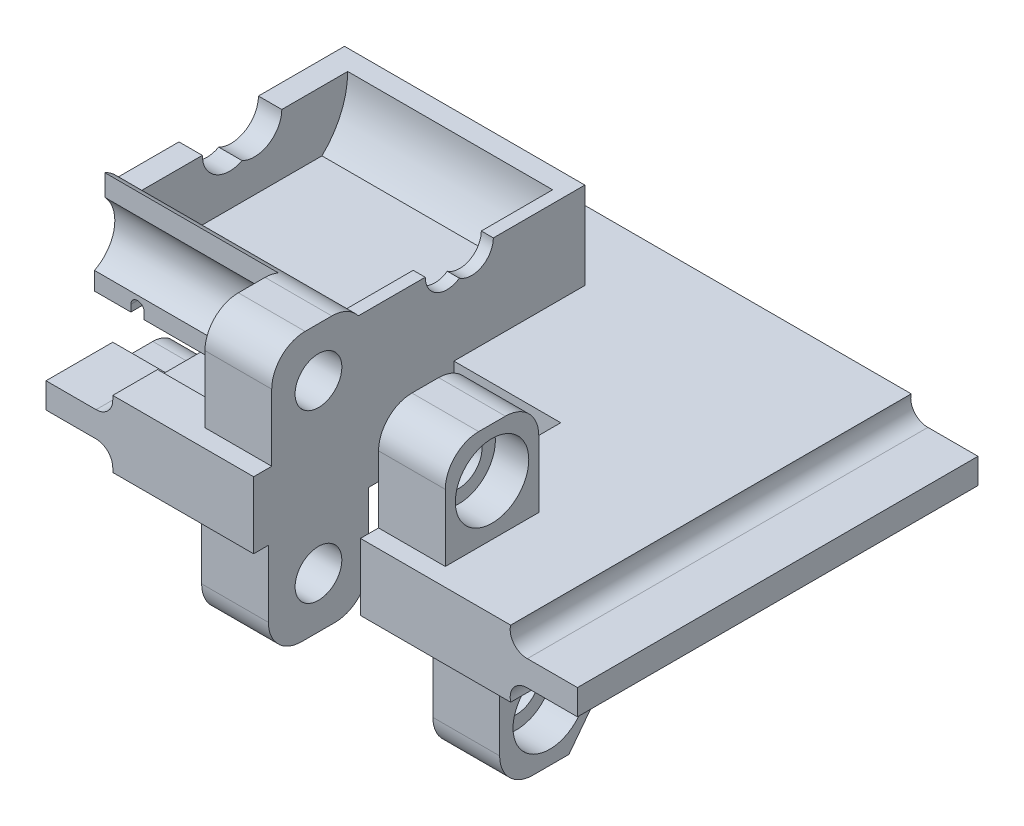
SolidWorks part; units mm, degrees
material "ABS"
ref_plane "정면" through (0, 0, 0) normal (0, 0, 1) x (1, 0, 0)
ref_plane "윗면" through (0, 0, 0) normal (0, 1, 0) x (1, 0, 0)
ref_plane "우측면" through (0, 0, 0) normal (1, 0, 0) x (0, 0, -1)
sketch "스케치1" plane through (0, 0, 0) normal (0, 0, 1) x (1, 0, 0)
  line L0 (0, 0) -> (0, 10)
  line L1 (29.8, 10) -> (-29.8, 10)
  line L2 (-32.3, 6.9) -> (-39.8, 6.9)
  line L3 (-39.8, 6.9) -> (-39.8, 3.1)
  line L4 (-39.8, 3.1) -> (-32.3, 3.1)
  line L5 (-29.8, 0) -> (29.8, 0)
  line L6 (39.8, 3.1) -> (32.3, 3.1)
  line L7 (39.8, 6.9) -> (39.8, 3.1)
  line L8 (32.3, 6.9) -> (39.8, 6.9)
  line L9 (-29.8, 10) -> (-29.8, 9.4)
  line L10 (-29.8, 0.6) -> (-29.8, 0)
  arc A2 (32.3, 3.1) -> (29.8, 0) centre (32.2267, 0.6011) ccw
  arc A3 (29.8, 10) -> (32.3, 6.9) centre (32.2267, 9.3989) ccw
  arc A5 (-32.3, 3.1) -> (-29.8, 0.6) centre (-32.3, 0.6) cw
  arc A6 (-29.8, 9.4) -> (-32.3, 6.9) centre (-32.3, 9.4) cw
  point P13 (0, 5)
  point P14 (-39.8, 5)
  dimension "D5" = 2.5
  dimension "D6" = 2.5
  dimension "D1" = 39.8
  dimension "D2" = 29.8
  dimension "D3" = 10
  dimension "D4" = 29.8
  dimension "D7" = 3.8
extrude "보스-돌출1" add sketch "스케치1" along normal blind 60
sketch "스케치2" plane through (-39.8, 0, 0) normal (-1, 0, 0) x (0, 0, 1)
  line L1 (44, 4) -> (50, 4)
  line L2 (50, 4) -> (50, 8)
  line L3 (16, 4) -> (10, 4)
  line L4 (50, 8) -> (10, 8)
  line L5 (30, 8) -> (30, 0)
  line L6 (20, 0) -> (40, 0)
  line L7 (60, 6.9) -> (60, 3.1) construction
  line L8 (10, 4) -> (10, 8)
  line L9 (60, 0) -> (0, 0) construction
  arc A0 (40, 0) -> (44, 4) centre (44, 0) cw
  arc A1 (20, 0) -> (16, 4) centre (16, 0) ccw
  line M12 (0, 3.1) -> (60, 3.1)
  line M14 (60, 6.9) -> (0, 6.9)
  dimension "D4" = 4
  dimension "D1" = 4
  dimension "D2" = 4
  dimension "D3" = 10
  dimension "D5" = 20
  dimension "D6" = 10
extrude "컷-돌출1" cut sketch "스케치2" against normal blind 17.3 contours A1 L5 L8 L3 M12 M14 | L6 A0 L5 M12 | A0 L1 L2 L5 M12 M14
sketch "Sketch1" plane through (0, 10, 0) normal (0, 1, 0) x (1, 0, 0)
  line L0 (29.8, -60) -> (-29.8, -60) construction
  line L1 (7.3, -60) -> (-8.7, -60)
  line L2 (7.3, -60) -> (7.3, -30)
  line L3 (7.3, -30) -> (-8.7, -30)
  line L4 (-8.7, -60) -> (-8.7, -30)
  line L5 (29.8, -60) -> (29.8, 0) construction
  dimension "D1" = 22.5
  dimension "D2" = 30
  dimension "D3" = 16
extrude "Cut-Extrude1" cut sketch "Sketch1" against normal blind 10
sketch "Sketch2" plane through (7.3, 0, 0) normal (-1, 0, 0) x (0, 0, 1)
  line L0 (60, 10) -> (30, 10) construction
  line L6 (57.29, 10) -> (43.29, 10)
  line L7 (57.29, 10) -> (57.29, 20)
  line L8 (52.29, 25) -> (48.29, 25)
  line L9 (43.29, 10) -> (43.29, 20)
  circle A0 centre (50.29, 17.61) radius 3.5
  arc A3 (48.29, 25) -> (43.29, 20) centre (48.29, 20) ccw
  arc A4 (57.29, 20) -> (52.29, 25) centre (52.29, 20) ccw
  point P1 (50.29, 25)
  point P11 (43.29, 25)
  point P15 (57.29, 25)
  dimension "D1" = 7
  dimension "D2" = 14
  dimension "D6" = 5
  dimension "D3" = 7.61
  dimension "D4" = 9.71
  dimension "D5" = 15
extrude "Boss-Extrude1" add sketch "Sketch2" against normal blind 10
sketch "Sketch4" plane through (17.3, 0, 0) normal (1, 0, 0) x (0, 0, -1)
  circle A0 centre (-50.29, 17.61) radius 5.5
  dimension "D1" = 11
extrude "Cut-Extrude4" cut sketch "Sketch4" against normal blind 5
ref_plane "Plane1" through (-0.7, 0, 0) normal (-1, 0, 0) x (0, 0, 1)
mirror "Mirror1" about plane through (-0.7, 0, 0) normal (-1, 0, 0) of "Cut-Extrude4", "Boss-Extrude1"
sketch "Sketch5" plane through (-8.7, 0, 0) normal (1, 0, 0) x (0, 0, -1)
  line L0 (-30, 0) -> (-60, 0) construction
  line L1 (-60, 0) -> (-60, 10) construction
  line L3 (-57.79, 0) -> (-42.79, 0)
  line L4 (-57.79, 0) -> (-57.79, -10)
  line L5 (-52.79, -15) -> (-47.79, -15)
  line L6 (-42.79, 0) -> (-42.79, -10)
  circle A0 centre (-50.29, -7.39) radius 3.5
  arc A1 (-47.79, -15) -> (-42.79, -10) centre (-47.79, -10) ccw
  arc A2 (-57.79, -10) -> (-52.79, -15) centre (-52.79, -10) ccw
  point P11 (-50.29, -15)
  point P14 (-42.79, -15)
  point P17 (-57.79, -15)
  dimension "D1" = 7
  dimension "D6" = 5
  dimension "D2" = 7.39
  dimension "D3" = 9.71
  dimension "D4" = 15
  dimension "D5" = 15
extrude "Boss-Extrude2" add sketch "Sketch5" against normal blind 10
sketch "Sketch6" plane through (-18.7, 0, 0) normal (-1, 0, 0) x (0, 0, 1)
  circle A0 centre (50.29, -7.39) radius 5.5
  dimension "D1" = 11
extrude "Cut-Extrude5" cut sketch "Sketch6" against normal blind 5
ref_plane "Plane2" through (3.62, 0, 0) normal (1, 0, 0) x (0, 0, -1)
mirror "Mirror2" about plane through (3.62, 0, 0) normal (1, 0, 0) of "Cut-Extrude5", "Boss-Extrude2"
sketch "Sketch7" plane through (-8.7, 0, 0) normal (1, 0, 0) x (0, 0, -1)
  line L0 (-30, 0) -> (-30, 10) construction
  line L1 (-30, 10) -> (-43.29, 10) construction
  line L2 (-40.0582, 14) -> (-17.2618, 14)
  line L4 (-39.4431, 32.6025) -> (-17.8769, 32.6025)
  line L8 (-46.1326, 23.0254) -> (-10.3854, 23.0254)
  line L9 (-46.1326, 36.0509) -> (-10.3854, 36.0509)
  line L10 (-46.1326, 36.0509) -> (-46.1326, 10)
  line L11 (-46.1326, 10) -> (-10.3854, 10)
  line L12 (-10.3854, 36.0509) -> (-10.3854, 10)
  arc A1 (-17.2618, 14) -> (-17.8769, 32.6025) centre (-25.91, 23.0254) ccw
  arc A2 (-39.4431, 32.6025) -> (-40.0582, 14) centre (-31.41, 23.0254) ccw
  dimension "D2" = 12.5
  dimension "D6" = 12.5
  dimension "D1" = 4.09
  dimension "D3" = 4
  dimension "D4" = 5.5
  dimension "D5" = 22.6025
extrude "Boss-Extrude4" add sketch "Sketch7" against normal blind 36
sketch "Sketch8" plane through (0, 23.0254, 0) normal (0, 1, 0) x (1, 0, 0)
  line L1 (-8.7, -13.41) -> (-10.5, -13.41)
  line L2 (-8.7, -13.41) -> (-8.7, -45.828)
  line L3 (-8.7, -45.828) -> (-10.5, -45.828)
  line L4 (-10.5, -13.41) -> (-10.5, -45.828)
  line L6 (-44.7, -13.41) -> (-41.2, -13.41)
  line L7 (-44.7, -13.41) -> (-44.7, -44.3767)
  line L8 (-44.7, -44.3767) -> (-41.2, -44.3767)
  line L9 (-41.2, -13.41) -> (-41.2, -44.3767)
  dimension "D1" = 1.8
  dimension "D2" = 3.5
extrude "Boss-Extrude5" add sketch "Sketch8" against normal blind 10
sketch "Sketch9" plane through (-8.7, 0, 0) normal (1, 0, 0) x (0, 0, -1)
  line L0 (-44.3092, 23.0254) -> (-10.3854, 23.0254) construction
  line L1 (-44.3092, 23.0254) -> (-10.3854, 23.0254) construction
  circle A0 centre (-27.3473, 23.0254) radius 3.25
  circle A1 centre (-31.0473, 23.0254) radius 3.25
  line M2 (-10.3854, 23.0254) -> (-44.3092, 23.0254)
  dimension "D1" = 6.5
  dimension "D2" = 6.5
  dimension "D3" = 3.7
extrude "Cut-Extrude6" cut sketch "Sketch9" against normal blind 10 contours A1 A0 M2 | A1 A0 M2
sketch "Sketch10" plane through (-44.7, 0, 0) normal (-1, 0, 0) x (0, 0, 1)
  line L0 (44.3767, 23.0254) -> (10.3854, 23.0254) construction
  line L1 (44.3767, 23.0254) -> (10.3854, 23.0254) construction
  circle A0 centre (27.3811, 23.0254) radius 4.1
  circle A1 centre (31.0811, 23.0254) radius 4.1
  line M10 (44.3767, 23.0254) -> (10.3854, 23.0254)
  dimension "D1" = 8.2
  dimension "D2" = 8.2
  dimension "D3" = 3.7
extrude "Cut-Extrude7" cut sketch "Sketch10" against normal blind 10 contours A1 A0 M10 | A1 A0 M10 | A0 A1 M10
sketch "Sketch12" plane through (25.94, 0, 0) normal (1, 0, 0) x (0, 0, -1)
  line L0 (-42.79, -8.9362) -> (-47.4024, -14.985)
  line L1 (-42.79, -10) -> (-42.79, 0) construction
  line L2 (-47.4024, -14.985) -> (-43.1675, -15.5436)
  line L3 (-43.1675, -15.5436) -> (-40.8892, -10)
  line L4 (-40.8892, -10) -> (-42.79, -8.9362)
  arc A0 (-47.79, -15) -> (-42.79, -10) centre (-47.79, -10) ccw construction
extrude "Cut-Extrude9" cut sketch "Sketch12" against normal blind 10
sketch "Sketch13" plane through (0, 0, 43.29) normal (0, 0, 1) x (1, 0, 0)
  line L0 (-29.8, 10) -> (-23.7804, 10)
  line L1 (-29.8, 10) -> (-18.7, 10) construction
  line L2 (-23.7804, 10) -> (-23.7804, 11.1029)
  line L3 (-21.7804, 11.1029) -> (-21.7804, 9)
  line L4 (-21.7804, 9) -> (-30.476, 9)
  line L5 (-30.476, 9) -> (-29.8, 10)
  arc A0 (-23.7804, 11.1029) -> (-21.7804, 11.1029) centre (-22.7804, 11.1029) cw
  dimension "D2" = 1
  dimension "D1" = 1
extrude "Cut-Extrude10" cut sketch "Sketch13" against normal blind 35 and the other way blind 10
sketch "Sketch11" plane through (0, 0, 43.29) normal (0, 0, 1) x (1, 0, 0)
  line L0 (-39.25, 10) -> (-39.25, 11)
  line L2 (-37.25, 11) -> (-37.25, 10)
  line L3 (-37.25, 10) -> (-39.25, 10)
  arc A0 (-39.25, 11) -> (-37.25, 11) centre (-38.25, 11) cw
  dimension "D1" = 1
  dimension "D2" = 1
  dimension "D3" = 2
extrude "Cut-Extrude8" cut sketch "Sketch11" against normal through all and the other way blind 24
sketch "Sketch14" plane through (-18.7, 0, 0) normal (-1, 0, 0) x (0, 0, 1)
  line L1 (47.8417, 12.685) -> (47.8417, 10)
  line L2 (43.29, 10) -> (57.29, 10) construction
  line L3 (47.8417, 10) -> (43.29, 10)
  line L4 (43.29, 10) -> (43.29, 20)
  circle A0 centre (50.29, 17.61) radius 5.5 construction
  arc A1 (46.2859, 21.3806) -> (47.8417, 12.685) centre (50.29, 17.61) ccw
sketch "Sketch17" plane through (-18.7, 0, 0) normal (-1, 0, 0) x (0, 0, 1)
  line L0 (43.29, 10) -> (47.8417, 10)
  line L1 (47.8417, 10) -> (47.8417, 12.685)
  line L2 (46.2859, 21.3806) -> (46.2859, 24.5808)
  line L3 (43.29, 20) -> (43.29, 10)
  arc A0 (47.8417, 12.685) -> (46.2859, 21.3806) centre (50.29, 17.61) cw
  arc A1 (48.29, 25) -> (43.29, 20) centre (48.29, 20) ccw construction
  arc A2 (46.2859, 24.5808) -> (43.29, 20) centre (48.29, 20) ccw
  arc A3 (46.2859, 21.3806) -> (47.8417, 12.685) centre (50.29, 17.61) ccw construction
extrude "Boss-Extrude8" add sketch "Sketch17" along normal up to surface (26 mm away) up to face at (-44.7, 17.1326, 31.5331)
sketch "Sketch16" plane through (-10.5, 0, 0) normal (-1, 0, 0) x (0, 0, 1)
  line L0 (39.21, 14) -> (40.0582, 14)
  line L1 (40.0582, 14) -> (17.2618, 14) construction
  line L2 (34.2973, 23.0254) -> (44.3092, 23.0254) construction
  line L3 (43.91, 23.0254) -> (41.1378, 23.0254)
  line L4 (41.1378, 23.0254) -> (39.21, 14)
  arc A0 (40.0582, 14) -> (43.91, 23.0254) centre (31.41, 23.0254) ccw
  arc A1 (40.0582, 14) -> (43.29, 19.1376) centre (31.41, 23.0254) ccw construction
extrude "Cut-Extrude12" cut sketch "Sketch16" along normal up to surface (30.7 mm away) up to face at (-41.2, 19.4189, 32.0509)
sketch "Sketch18" plane through (0, 0, 43.29) normal (0, 0, -1) x (-1, 0, 0)
  line L6 (21.7804, 11.1029) -> (21.7804, 10)
  line L7 (21.7804, 10) -> (23.7804, 10)
  line L8 (23.7804, 10) -> (23.7804, 11.1029)
  line L9 (21.7804, 11.1029) -> (21.7804, 10)
  line L10 (21.7804, 10) -> (23.7804, 10)
  line L11 (23.7804, 10) -> (23.7804, 11.1029)
  arc A2 (23.7804, 11.1029) -> (21.7804, 11.1029) centre (22.7804, 11.1029) ccw
  arc A3 (23.7804, 11.1029) -> (21.7804, 11.1029) centre (22.7804, 11.1029) ccw
  dimension "D1" = 0
extrude "Cut-Extrude13" cut sketch "Sketch18" against normal up to surface (4.5517 mm away) up to face at (-29.7161, 11.074, 47.8417)
sketch "Sketch19" plane through (0, 0, 43.29) normal (0, 0, -1) x (-1, 0, 0)
  line L6 (37.25, 11) -> (37.25, 10)
  line L7 (37.25, 10) -> (39.25, 10)
  line L8 (39.25, 10) -> (39.25, 11)
  line L9 (37.25, 11) -> (37.25, 10)
  line L10 (37.25, 10) -> (39.25, 10)
  line L11 (39.25, 10) -> (39.25, 11)
  arc A2 (39.25, 11) -> (37.25, 11) centre (38.25, 11) ccw
  arc A3 (39.25, 11) -> (37.25, 11) centre (38.25, 11) ccw
  dimension "D1" = 0
extrude "Cut-Extrude14" cut sketch "Sketch19" against normal blind 14
